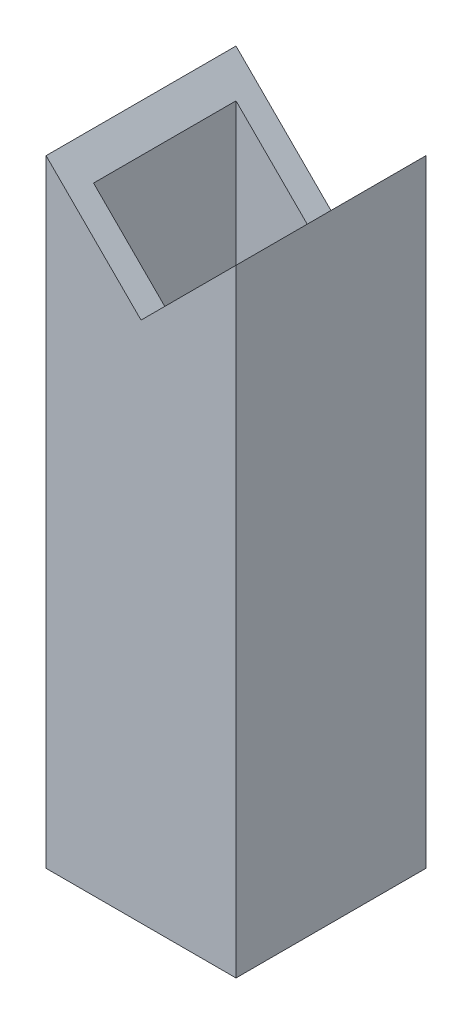
SolidWorks part; units mm, degrees
ref_plane "Front Plane" through (0, 0, 0) normal (0, 0, 1) x (1, 0, 0)
ref_plane "Top Plane" through (0, 0, 0) normal (0, 1, 0) x (1, 0, 0)
ref_plane "Right Plane" through (0, 0, 0) normal (1, 0, 0) x (0, 0, -1)
sketch "Sketch1" plane through (0, 0, 0) normal (0, 1, 0) x (1, 0, 0)
  line L1 (-25.4, -25.4) -> (25.4, -25.4)
  line L2 (-25.4, -25.4) -> (-25.4, 25.4)
  line L3 (-25.4, 25.4) -> (25.4, 25.4)
  line L4 (25.4, -25.4) -> (25.4, 25.4)
  line L5 (-25.4, -25.4) -> (25.4, 25.4) construction
  line L6 (-25.4, 25.4) -> (25.4, -25.4) construction
  line L7 (-19.05, -19.05) -> (19.05, -19.05)
  line L8 (-19.05, -19.05) -> (-19.05, 19.05)
  line L9 (-19.05, 19.05) -> (19.05, 19.05)
  line L10 (19.05, -19.05) -> (19.05, 19.05)
  line L11 (-19.05, -19.05) -> (19.05, 19.05) construction
  line L12 (-19.05, 19.05) -> (19.05, -19.05) construction
  point P0 (0, 0)
  point P6 (0, 0)
  dimension "D1" = 6.35
  dimension "D2" = 6.35
  dimension "D3" = 50.8
extrude "Boss-Extrude1" add sketch "Sketch1" along normal mid plane 165.1
sketch "Sketch3" plane through (0, 0, 25.4) normal (0, 0, 1) x (1, 0, 0)
  line L0 (-25.4, 82.55) -> (0, 57.15)
  line L1 (0, 57.15) -> (25.4, 82.55)
  dimension "D1" = 90
extrude "Cut-Extrude1" cut sketch "Sketch3" against normal through all and the other way through all
equation "\"D2@Sketch1\" = \"D1@Sketch1\""
